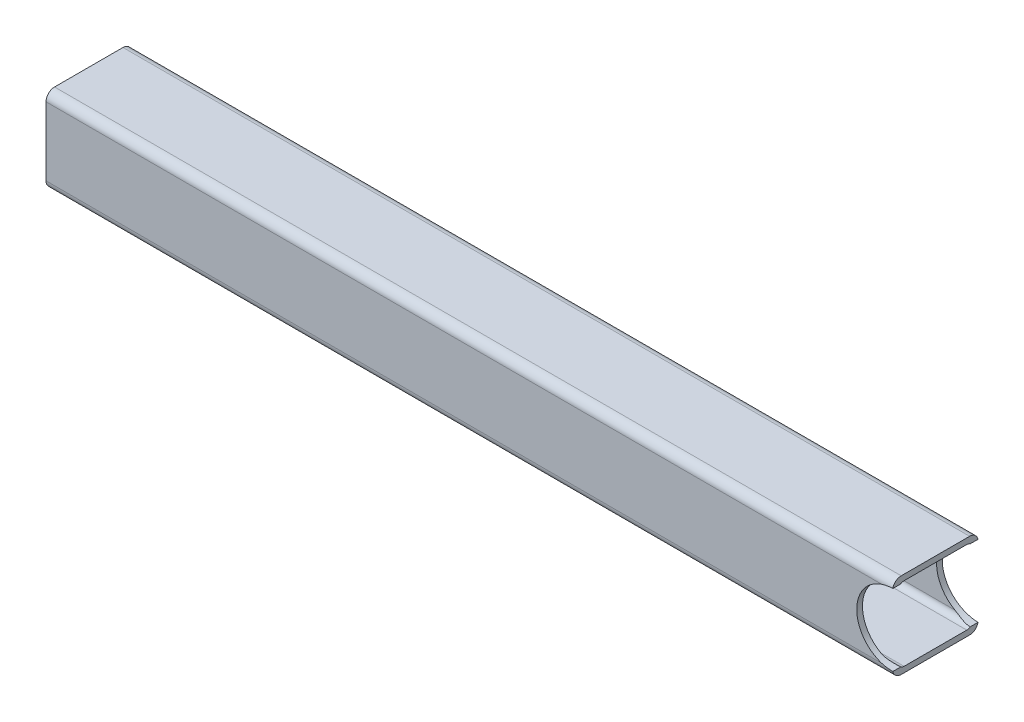
SolidWorks part; units mm, degrees
material "AISI 1020"
ref_plane "Спереди" through (0, 0, 0) normal (0, 0, 1) x (1, 0, 0)
ref_plane "Сверху" through (0, 0, 0) normal (0, 1, 0) x (1, 0, 0)
ref_plane "Справа" through (0, 0, 0) normal (1, 0, 0) x (0, 0, -1)
sketch "Эскиз1" plane through (0, 0, 0) normal (1, 0, 0) x (0, 0, -1)
  line B0 (-12, 15) -> (12, 15)
  line B1 (-15, 12) -> (-15, -12)
  line B2 (-12, -15) -> (12, -15)
  line B3 (15, 12) -> (15, -12)
  line B4 (-11, 13) -> (11, 13)
  line B5 (-13, 11) -> (-13, -11)
  line B6 (-11, -13) -> (11, -13)
  line B7 (13, 11) -> (13, -11)
  arc B8 (-15, -12) -> (-12, -15) centre (-12, -12) ccw
  arc B9 (12, -15) -> (15, -12) centre (12, -12) ccw
  arc B10 (12, 15) -> (15, 12) centre (12, 12) cw
  arc B11 (-12, 15) -> (-15, 12) centre (-12, 12) ccw
  arc B12 (-13, -11) -> (-11, -13) centre (-11, -11) ccw
  arc B13 (11, -13) -> (13, -11) centre (11, -11) ccw
  arc B14 (11, 13) -> (13, 11) centre (11, 11) cw
  arc B15 (-11, 13) -> (-13, 11) centre (-11, 11) ccw
sketch_block_instance "Блок-30х30х2-1"
sketch_block "Блок-30х30х2" parameters "D3"=3, "D4"=2, "D1"=30, "D2"=2
extrude "Бобышка-Вытянуть1" add sketch "Эскиз1" against normal offset from surface (297.0168 mm away) 180
other "Полость1"
other "ТП.016.000 - Проект бортового модуля<1>@ТП.016.0000 - X-REX (фронтальный заезд)/Проект оси катков<3>@ТП.016.000 - Проект бортового модуля/ТП.016.02.01.01.02 - Ось<1>@Проект оси катков"
sketch "Эскиз2" plane through (0, 0, 15) normal (0, 0, 1) x (1, 0, 0)
  circle A0 centre (0, 0) radius 12.6
  dimension "D1" = 25.2
extrude "Вырез-Вытянуть1" cut sketch "Эскиз2" against normal through all
